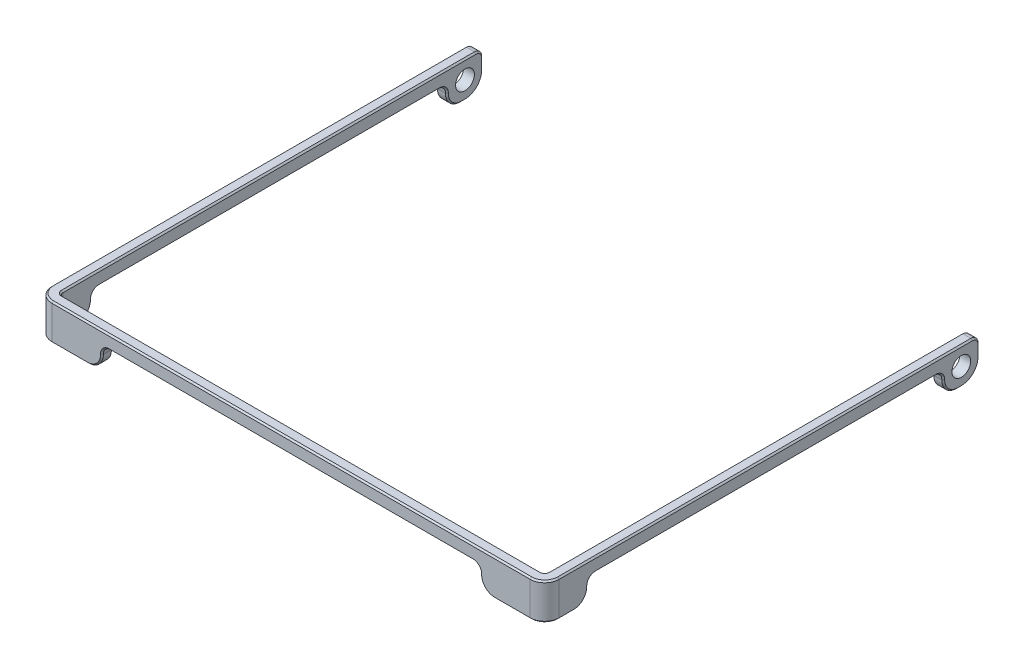
SolidWorks part; units mm, degrees
ref_plane "前视基准面" through (0, 0, 0) normal (0, 0, 1) x (1, 0, 0)
ref_plane "上视基准面" through (0, 0, 0) normal (0, 1, 0) x (1, 0, 0)
ref_plane "右视基准面" through (0, 0, 0) normal (1, 0, 0) x (0, 0, -1)
sketch "草图1" plane through (0, 0, 0) normal (0, 1, 0) x (1, 0, 0)
  line L0 (33.5, 29.25) -> (35, 29.25)
  line L2 (-33.5, 29.25) -> (-33.5, -29.25)
  line L3 (-33.5, -29.25) -> (33.5, -29.25)
  line L4 (33.5, 29.25) -> (33.5, -29.25)
  line L5 (-33.5, 29.25) -> (33.5, -29.25) construction
  line L6 (-33.5, -29.25) -> (33.5, 29.25) construction
  line L7 (-35, 29.25) -> (-33.5, 29.25)
  line L8 (-35, 29.25) -> (-35, -30.75)
  line L9 (-35, -30.75) -> (35, -30.75)
  line L10 (35, 29.25) -> (35, -30.75)
  point P0 (0, 0)
  dimension "D1" = 67
  dimension "D2" = 58.5
  dimension "D3" = 1.5
  dimension "D4" = 1.5
  dimension "D5" = 1.5
extrude "凸台-拉伸1" add sketch "草图1" along normal blind 5
fillet "圆角1" radius 2 2 edges at (35, 2.5, 30.75) (-35, 2.5, 30.75)
fillet "圆角2" radius 0.5 2 edges at (33.5, 2.5, 29.25) (-33.5, 2.5, 29.25)
fillet "圆角3" radius 2.5 2 edges at (34.25, 0, -29.25) (-34.25, 0, -29.25)
sketch "草图2" plane through (-35, 0, 0) normal (-1, 0, 0) x (0, 0, 1)
  line L0 (-29.25, 5) -> (28.75, 5) construction
  line L1 (-29.25, 5) -> (-29.25, 2.5) construction
  circle A0 centre (-26.75, 2.5) radius 1.3
  dimension "D1" = 2.6
  dimension "D2" = 2.5
  dimension "D3" = 2.5
extrude "切除-拉伸1" cut sketch "草图2" against normal blind 100
sketch "草图3" plane through (0, 0, 30.75) normal (0, 0, 1) x (1, 0, 0)
  line L0 (-33, 0) -> (33, 0) construction
  line L1 (-26.1, 3.1) -> (26.1, 3.1)
  line L2 (-26.1, 3.1) -> (-26.1, -3.1)
  line L3 (-26.1, -3.1) -> (26.1, -3.1)
  line L4 (26.1, 3.1) -> (26.1, -3.1)
  line L5 (-26.1, 3.1) -> (26.1, -3.1) construction
  line L6 (-26.1, -3.1) -> (26.1, 3.1) construction
  point P0 (0, 0)
  dimension "D1" = 52.2
  dimension "D2" = 3.1
extrude "切除-拉伸2" cut sketch "草图3" against normal blind 5
fillet "圆角5" radius 1 2 edges at (26.1, 3.1, 30) (-26.1, 3.1, 30)
sketch "草图4" plane through (-35, 0, 0) normal (-1, 0, 0) x (0, 0, 1)
  line L0 (-29.25, 5) -> (-29.25, 2.5) construction
  line L1 (-24.25, 3.1) -> (24.75, 3.1)
  line L2 (-24.25, 3.1) -> (-24.25, -5.7207)
  line L3 (-24.25, -5.7207) -> (24.75, -5.7207)
  line L4 (24.75, 3.1) -> (24.75, -5.7207)
  line L5 (30.75, 5) -> (30.75, 0) construction
  line L6 (-29.25, 5) -> (28.75, 5) construction
  dimension "D1" = 5
  dimension "D2" = 6
  dimension "D3" = 1.9
extrude "切除-拉伸3" cut sketch "草图4" against normal blind 100
fillet "圆角6" radius 1 6 edges at (34.25, 3.1, 24.75) (-34.25, 3.1, 24.75) (-34.25, 3.1, -24.25) (34.25, 3.1, -24.25) (-34.25, 5, -29.25) (34.25, 5, -29.25)
fillet "圆角7" radius 2 6 edges at (-34.25, 0, 24.75) (-26.1, 0, 30) (26.1, 0, 30) (34.25, 0, 24.75) (34.25, 0, -24.25) (-34.25, 0, -24.25)
chamfer "倒角1" distance 0.2 angle 45 80 edges at (26.1, 2.05, 29.25) (26.6858, 0.5858, 29.25) (25.8071, 2.8071, 29.25) (30.55, 0, 29.25) (0, 3.1, 29.25) (33.3536, 0, 29.1036) (-25.8071, 2.8071, 29.25) (33.5, 0, 27.75) (-26.1, 2.05, 29.25) (33.5, 0.5858, 25.3358) (-26.6858, 0.5858, 29.25) (33.5, 2.05, 24.75) (-30.55, 0, 29.25) (33.5, 2.8071, 24.4571) (-33.3536, 0, 29.1036) (33.5, 3.1, 0.25) (-33.5, 0, 27.75) (33.5, 2.8071, -23.9571) (-33.5, 0.5858, 25.3358) (33.5, 2.05, -24.25) (-33.5, 2.05, 24.75) (33.5, 0.5858, -24.8358) (-33.5, 2.8071, 24.4571) (33.5, 0, -26.5) (-33.5, 3.1, 0.25) (33.5, 0.7322, -28.5178) (-33.5, 2.8071, -23.9571) (33.5, 3.25, -29.25) (-33.5, 2.05, -24.25) (33.5, 4.7071, -28.9571) (-33.5, 0.5858, -24.8358) (33.5, 5, 0.25) (-33.5, 0, -26.5) (33.3536, 5, 29.1036) (-33.5, 0.7322, -28.5178) (0, 5, 29.25) (-33.5, 3.25, -29.25) (-33.3536, 5, 29.1036) (-33.5, 4.7071, -28.9571) (-33.5, 5, 0.25) (26.1, 2.05, 30.75) (25.8071, 2.8071, 30.75) (26.6858, 0.5858, 30.75) (0, 3.1, 30.75) (30.55, 0, 30.75) (-25.8071, 2.8071, 30.75) (34.4142, 0, 30.1642) (-26.1, 2.05, 30.75) (35, 0, 27.75) (-26.6858, 0.5858, 30.75) (35, 0.5858, 25.3358) (-30.55, 0, 30.75) (35, 2.05, 24.75) (-34.4142, 0, 30.1642) (35, 2.8071, 24.4571) (-35, 0, 27.75) (35, 3.1, 0.25) (-35, 0.5858, 25.3358) (35, 2.8071, -23.9571) (-35, 2.05, 24.75) (35, 2.05, -24.25) (-35, 2.8071, 24.4571) (35, 0.5858, -24.8358) (-35, 3.1, 0.25) (35, 0, -26.5) (-35, 2.8071, -23.9571) (35, 0.7322, -28.5178) (-35, 2.05, -24.25) (35, 3.25, -29.25) (-35, 0.5858, -24.8358) (35, 4.7071, -28.9571) (-35, 0, -26.5) (35, 5, 0.25) (-35, 0.7322, -28.5178) (34.4142, 5, 30.1642) (-35, 3.25, -29.25) (0, 5, 30.75) (-35, 4.7071, -28.9571) (-34.4142, 5, 30.1642) (-35, 5, 0.25)
